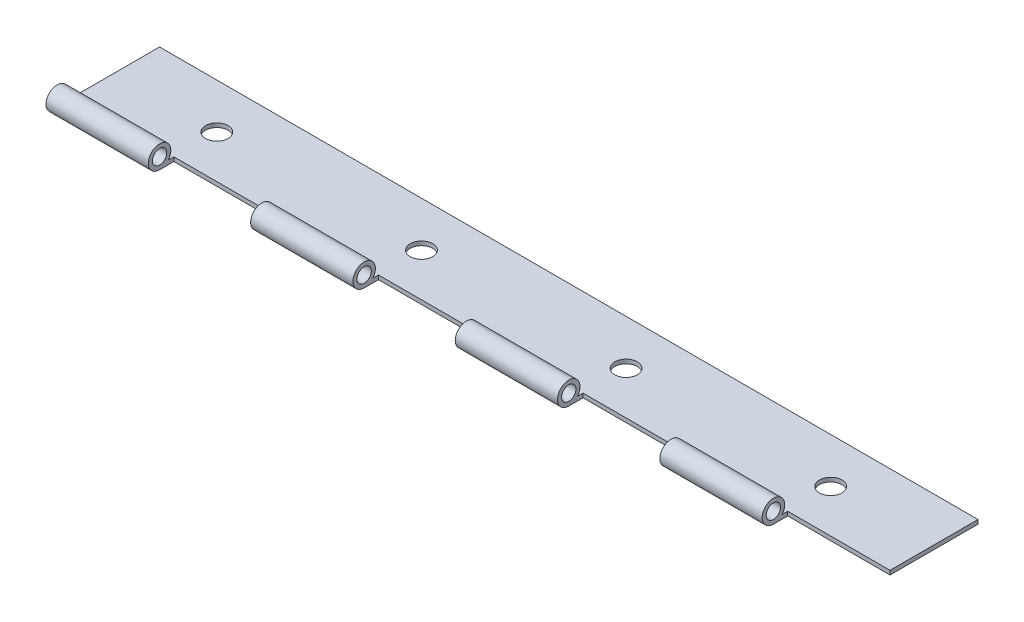
SolidWorks part; units mm, degrees
ref_plane "Front Plane" through (0, 0, 0) normal (0, 0, 1) x (1, 0, 0)
ref_plane "Top Plane" through (0, 0, 0) normal (0, 1, 0) x (1, 0, 0)
ref_plane "Right Plane" through (0, 0, 0) normal (1, 0, 0) x (0, 0, -1)
sketch "Sketch1" plane through (0, 0, 0) normal (1, 0, 0) x (0, 0, -1)
  line L0 (0, -2.794) -> (25.4, -2.794)
  line L1 (25.4, -2.794) -> (25.4, -1.778)
  line L2 (25.4, -1.778) -> (2.1553, -1.778)
  circle A0 centre (0, 0) radius 1.778
  arc A1 (2.1553, -1.778) -> (0, -2.794) centre (0, 0) ccw
  dimension "D1" = 3.556
  dimension "D2" = 5.588
  dimension "D3" = 1.016
  dimension "D4" = 25.4
extrude "Boss-Extrude1" add sketch "Sketch1" along normal mid plane 203.2 contours L0 L1 L2 A1 | A0
sketch "Sketch2" plane through (0, -1.778, 0) normal (0, 1, 0) x (1, 0, 0)
  line L0 (101.6, 25.4) -> (-101.6, 25.4) construction
  line L1 (-101.6, -2.794) -> (101.6, -2.794) construction
  line L2 (-25.4, -2.794) -> (0, -2.794)
  line L3 (-25.4, -2.794) -> (-25.4, 3.556)
  line L4 (-25.4, 3.556) -> (0, 3.556)
  line L5 (0, -2.794) -> (0, 3.556)
  circle A0 centre (-25.4, 14.224) radius 2.794
  dimension "D1" = 5.588
  dimension "D3" = 25.4
  dimension "D2" = 11.176
  dimension "D4" = 6.35
  dimension "D5" = 25.4
extrude "Cut-Extrude1" cut sketch "Sketch2" against normal mid plane 1828.8
pattern_linear "LPattern1" count 3 spacing 50.8 along (-1, 0, 0) of "Cut-Extrude1"
pattern_linear "LPattern2" count 3 spacing 50.8 along (1, 0, 0) of "Cut-Extrude1"
equation "\"HingeLength\"=8"
equation "\"HoleSpace\"= 2"
equation "\"CutLength\"= 1"
equation "\"D1@Boss-Extrude1\"=\"HingeLength\""
equation "\"D3@Sketch2\"=\"HoleSpace\"/2"
equation "\"D5@Sketch2\"=\"CutLength\""
equation "\"D3@LPattern1\"=\"HoleSpace\""
equation "\"D1@LPattern1\"=((\"HingeLength\"/2)/\"HoleSpace\")+1"
equation "\"D3@LPattern2\"=\"HoleSpace\""
equation "\"D1@LPattern2\"=((\"HingeLength\"/2)/\"HoleSpace\")+1"
